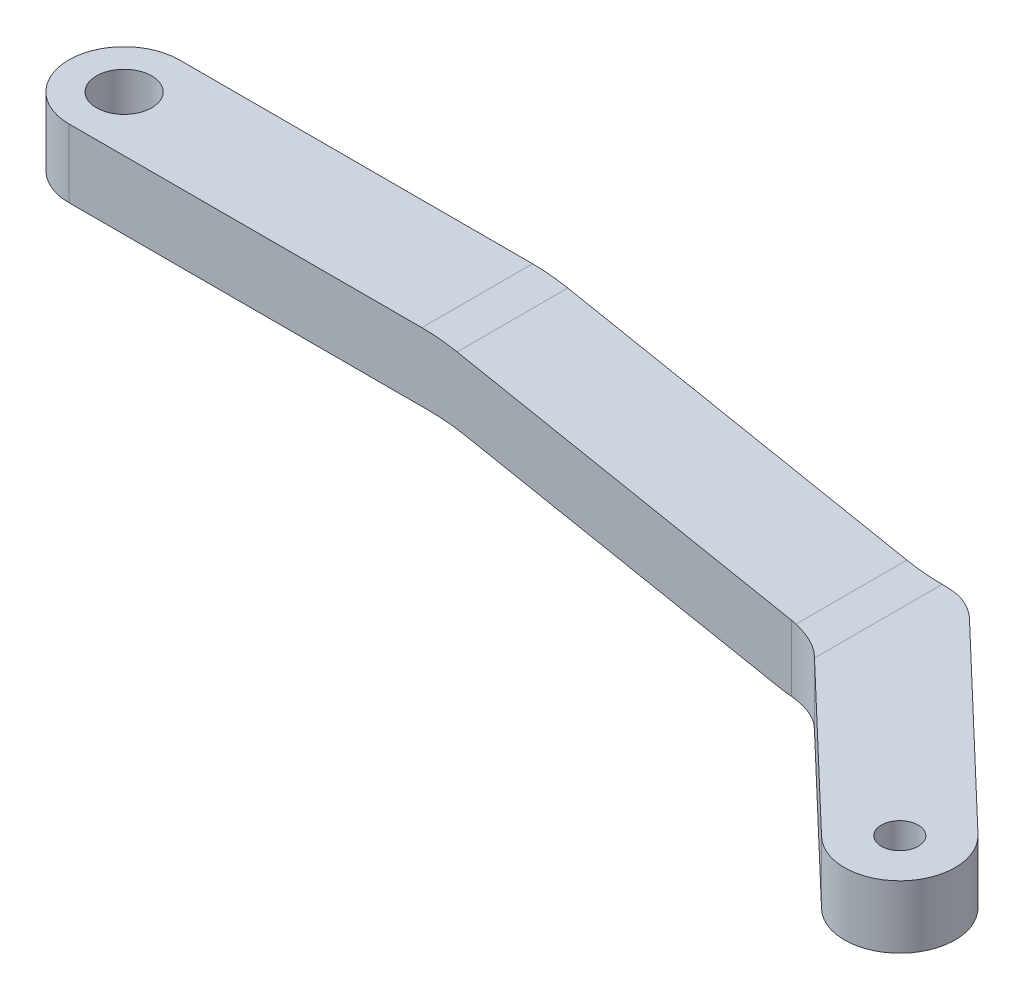
SolidWorks part; units mm, degrees
ref_plane "Front Plane" through (0, 0, 0) normal (0, 0, 1) x (1, 0, 0)
ref_plane "Top Plane" through (0, 0, 0) normal (0, 1, 0) x (1, 0, 0)
ref_plane "Right Plane" through (0, 0, 0) normal (1, 0, 0) x (0, 0, -1)
sketch "Sketch1" plane through (0, 0, 0) normal (0, 0, 1) x (1, 0, 0)
  line L0 (-14.712, 3.95) -> (8.398, 3.95)
  line L1 (8.398, 3.95) -> (28.678, 0)
  line L2 (28.678, 0) -> (-14.712, 0)
  line L3 (-14.712, 0) -> (-14.712, 3.95)
  dimension "D1" = 3.95
  dimension "D2" = 43.39
  dimension "D3" = 23.11
extrude "Boss-Extrude1" add sketch "Sketch1" along normal mid plane 6
sketch "Sketch2" plane through (0, 0, 0) normal (0, -1, 0) x (1, 0, 0)
  line L4 (-14.712, -3) -> (28.678, -3)
  line L5 (28.678, -3) -> (28.678, 3)
  line L6 (28.678, 3) -> (-14.712, 3)
  line L7 (-14.712, 3) -> (-14.712, -3)
  line L8 (-11.712, -3) -> (31.0833, -3)
  line L10 (28.678, 3) -> (-11.712, 3)
  line L12 (28.678, 3) -> (38.2227, 12.118)
  line L14 (-14.712, 3) -> (-14.712, -3) construction
  line L15 (42.3673, 7.7795) -> (31.0833, -3)
  arc A3 (-11.712, 3) -> (-11.712, -3) centre (-11.712, 0) ccw
  arc A4 (42.3673, 7.7795) -> (38.2227, 12.118) centre (40.295, 9.9487) ccw
  dimension "D11" = 13.2
  dimension "D10" = 6
  dimension "D9" = 136.31
  dimension "D1" = 0
extrude "Boss-Extrude2" add sketch "Sketch2" along normal blind 3.4
sketch "Sketch3" plane through (0, 3.95, 0) normal (0, 1, 0) x (1, 0, 0)
  line L4 (8.398, 3) -> (-14.712, 3)
  line L5 (-14.712, 3) -> (-14.712, -3)
  line L6 (-14.712, -3) -> (8.398, -3)
  line L7 (8.398, -3) -> (8.398, 3)
  line L8 (-11.712, 3) -> (-14.712, 3)
  line L9 (-14.712, 3) -> (-14.712, -3)
  line L10 (-14.712, -3) -> (-11.712, -3)
  line L11 (8.398, -3) -> (8.398, 3)
  arc A0 (-11.712, 3) -> (-11.712, -3) centre (-11.712, 0) ccw
  line M5 (8.398, 3) -> (-14.712, 3)
  line M6 (-14.712, 3) -> (-14.712, -3)
  line M7 (-14.712, -3) -> (8.398, -3)
  dimension "D1" = 0
extrude "Cut-Extrude1" cut sketch "Sketch3" against normal through all both and the other way through all contours A0 M5 M6 | A0 L9 M7
sketch "Sketch4" plane through (0, 0, 3) normal (0, 0, 1) x (1, 0, 0)
  line L0 (-14.712, 0.25) -> (8.8256, 0.25)
  line L1 (-14.712, 3.95) -> (-14.712, -3.4) construction
  line L2 (8.8256, 0.25) -> (27.5653, -3.4)
  line L3 (28.678, -3.4) -> (-11.712, -3.4) construction
  line L4 (27.5653, -3.4) -> (-14.712, -3.4)
  line L5 (-14.712, -3.4) -> (-11.712, -3.4) construction
  line L6 (-14.712, -3.4) -> (-14.712, 0.25)
  line L7 (8.398, 3.95) -> (-11.712, 3.95) construction
  line L8 (28.678, 0) -> (8.398, 3.95) construction
  dimension "D1" = 3.7
  dimension "D2" = 3.55
extrude "Cut-Extrude2" cut sketch "Sketch4" against normal through all both
sketch "Sketch6" plane through (0, 3.95, 0) normal (0, 1, 0) x (1, 0, 0)
  circle A0 centre (-11.712, 0) radius 1.5
  arc A1 (-11.712, 3) -> (-11.712, -3) centre (-11.712, 0) ccw construction
  circle A2 centre (40.295, -9.9487) radius 1
  arc A3 (38.2227, -12.118) -> (42.3673, -7.7795) centre (40.295, -9.9487) ccw construction
  dimension "D1" = 3
  dimension "D2" = 2
extrude "Cut-Extrude4" cut sketch "Sketch6" against normal through all both
fillet "Fillet1" radius 10 4 edges at (28.678, 0, 0) (8.398, 3.95, 0) (27.5653, -3.4, 0) (8.8256, 0.25, 0)
fillet "Fillet2" radius 3 2 edges at (31.0833, -1.7, -3) (28.678, -1.6767, 3)
